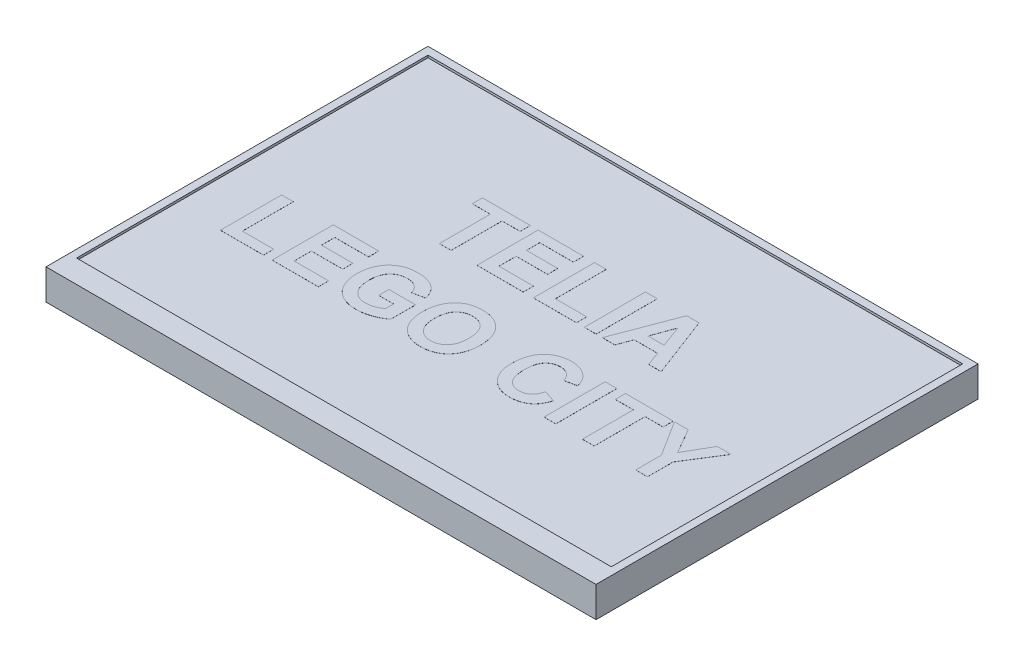
SolidWorks part; units mm, degrees
ref_plane "Front Plane" through (0, 0, 0) normal (0, 0, 1) x (1, 0, 0)
ref_plane "Top Plane" through (0, 0, 0) normal (0, 1, 0) x (1, 0, 0)
ref_plane "Right Plane" through (0, 0, 0) normal (1, 0, 0) x (0, 0, -1)
sketch "Sketch1" plane through (0, 0, 0) normal (0, 1, 0) x (1, 0, 0)
  line L1 (-360, 250) -> (360, 250)
  line L2 (-360, 250) -> (-360, -250)
  line L3 (-360, -250) -> (360, -250)
  line L4 (360, 250) -> (360, -250)
  line L5 (-360, 250) -> (360, -250) construction
  line L6 (-360, -250) -> (360, 250) construction
  point P0 (0, 0)
  dimension "D1" = 720
  dimension "D2" = 500
extrude "Boss-Extrude1" add sketch "Sketch1" along normal blind 40
sketch "Sketch2" plane through (0, 40, 0) normal (0, 1, 0) x (1, 0, 0)
  line L0 (0, -250) -> (0, 250) construction
  line L1 (-360, -250) -> (360, -250) construction
  line L2 (360, 250) -> (-360, 250) construction
  line L3 (-360, 250) -> (-360, -250) construction
  line L4 (350, -220) -> (-350, -220)
  line L5 (350, -220) -> (350, 240)
  line L6 (350, 240) -> (-350, 240)
  line L7 (-350, -220) -> (-350, 240)
  line L8 (350, -220) -> (-350, 240) construction
  line L9 (350, 240) -> (-350, -220) construction
  point P6 (0, 10)
  dimension "D1" = 10
  dimension "D2" = 10
  dimension "D3" = 30
extrude "Cut-Extrude1" cut sketch "Sketch2" against normal blind 3
sketch "Sketch3" plane through (0, 37, 0) normal (0, 1, 0) x (1, 0, 0)
  line L0 (-350, 36.7878) -> (350, 36.7878) construction
  line L3 (-350, 240) -> (-350, -220) construction
  line L4 (350, -220) -> (350, 240) construction
  text T0 "TELIA\r\nLEGO CITY" font "Arial" height 80
  point P3 (-282.573, 6.931)
  point P4 (-350, 10)
  point P5 (-316.1619, 10)
  point P6 (0, 0)
  point P7 (350, 10)
  point P8 (-350, 45.8515)
  point P10 (-350, 10)
  point P12 (350, 44.7852)
extrude "Boss-Extrude2" add sketch "Sketch3" along normal blind 0.1
